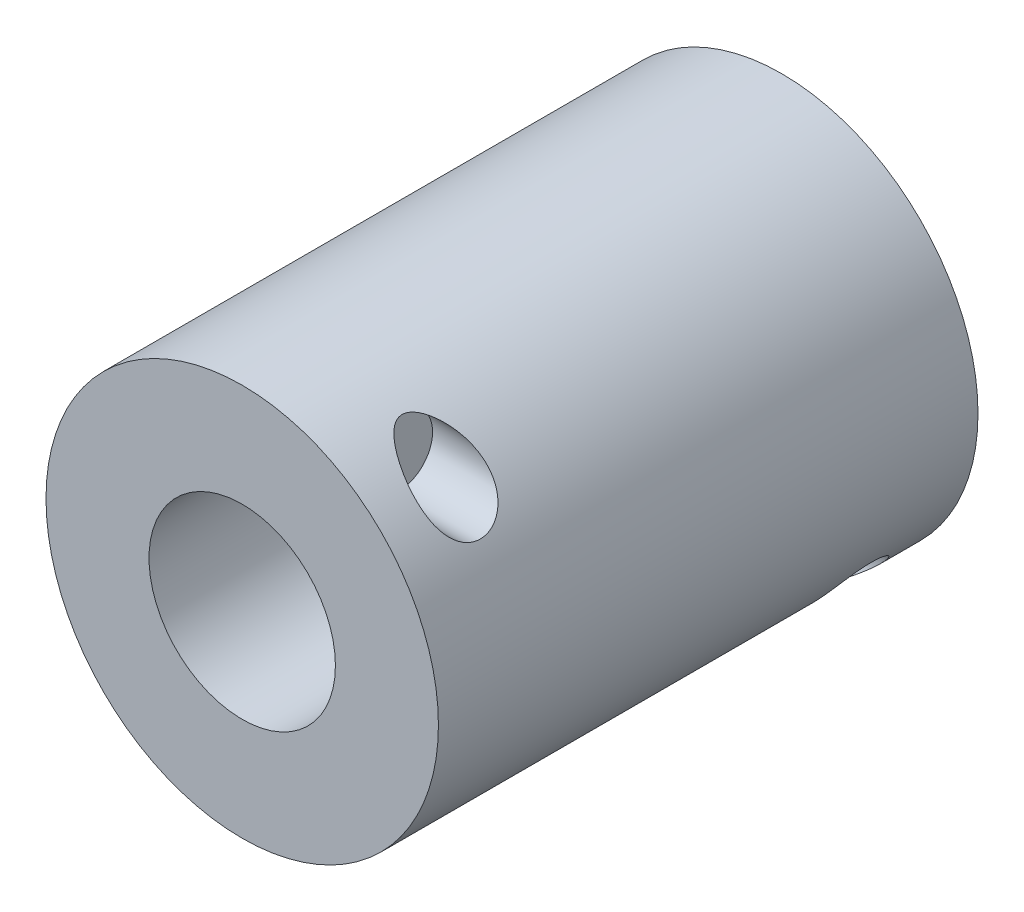
SolidWorks part; units mm, degrees
ref_plane "Front" through (0, 0, 0) normal (0, 0, 1) x (1, 0, 0)
ref_plane "Top" through (0, 0, 0) normal (0, 1, 0) x (1, 0, 0)
ref_plane "Right" through (0, 0, 0) normal (1, 0, 0) x (0, 0, -1)
sketch "Sketch1" plane through (0, 0, 0) normal (0, 0, 1) x (1, 0, 0)
  circle A0 centre (0, 0) radius 20
  circle A1 centre (0, 0) radius 9.5
  dimension "D1" = 19
  dimension "D2" = 40
extrude "Boss-Extrude1" add sketch "Sketch1" along normal blind 55
ref_plane "Plane1" through (8.3333, 0, 0) normal (1, 0, 0) x (0, 0, -1)
sketch "Sketch2" plane through (8.3333, 0, 0) normal (1, 0, 0) x (0, 0, -1)
  line L0 (-55, 20) -> (-47.4288, 14.4937)
  line L1 (-47.4288, 14.4937) -> (-7.5712, -14.4937)
  line L2 (-7.5712, -14.4937) -> (0, -20)
  circle A0 centre (-47.4288, 14.4937) radius 3.5
  circle A1 centre (-7.5712, -14.4937) radius 3.5
  dimension "D1" = 7
extrude "Cut-Extrude1" cut sketch "Sketch2" along normal through all contours A0 | A1
